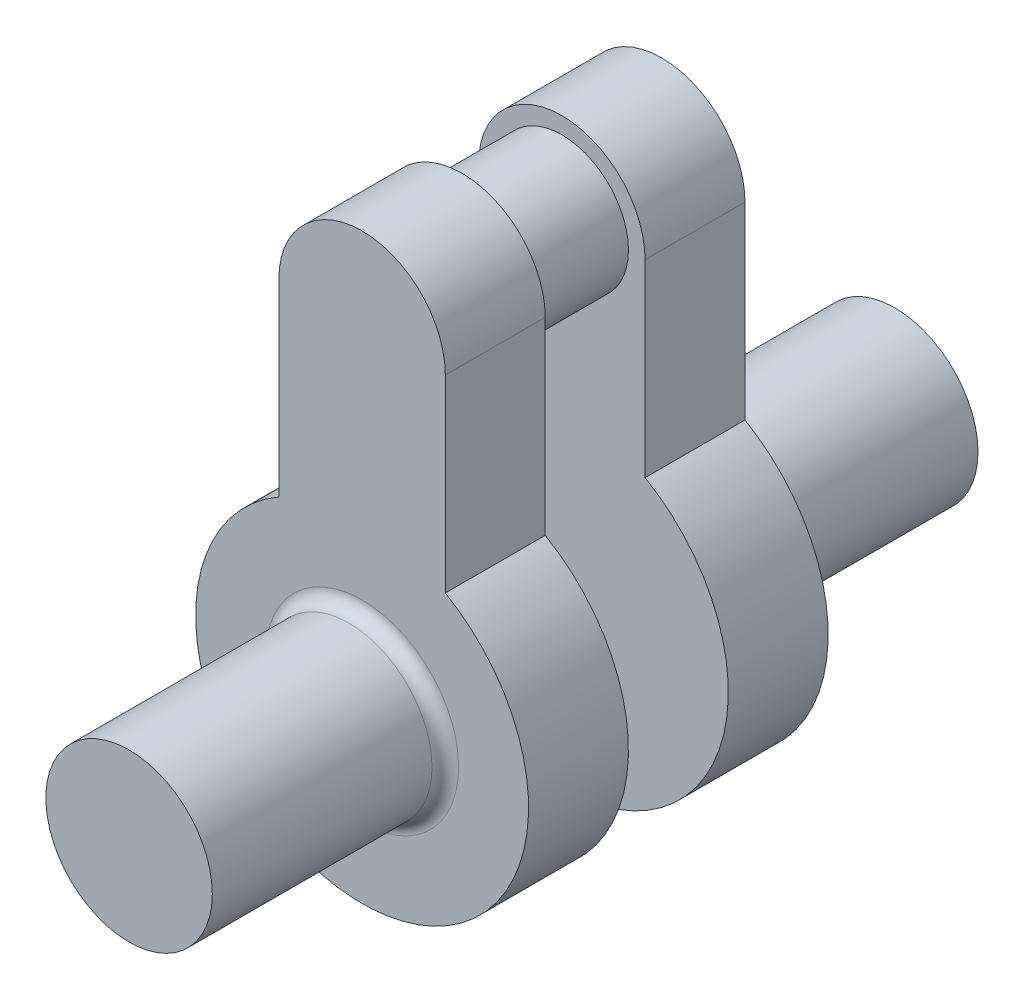
SolidWorks part; units mm, degrees
ref_plane "Ön Düzlem" through (0, 0, 0) normal (0, 0, 1) x (1, 0, 0)
ref_plane "Üst Düzlem" through (0, 0, 0) normal (0, 1, 0) x (1, 0, 0)
ref_plane "Sağ Düzlem" through (0, 0, 0) normal (1, 0, 0) x (0, 0, -1)
sketch "Sketch1" plane through (0, 0, 0) normal (0, 0, 1) x (1, 0, 0)
  line L0 (-12.5, 50) -> (-12.5, 21.6506)
  line L1 (12.5, 50) -> (12.5, 21.6506)
  arc A0 (-12.5, 21.6506) -> (12.5, 21.6506) centre (0, 0) ccw
  arc A3 (12.5, 50) -> (-12.5, 50) centre (0, 50) ccw
  dimension "D1" = 50
  dimension "D2" = 25
  dimension "D3" = 50
extrude "Boss-Extrude1" add sketch "Sketch1" along normal blind 15
sketch "Sketch2" plane through (0, 0, 15) normal (0, 0, 1) x (1, 0, 0)
  circle A0 centre (0, 0) radius 12.5
  dimension "D1" = 25
extrude "Boss-Extrude2" add sketch "Sketch2" along normal blind 35
fillet "Fillet1" radius 2 1 edges at (12.5, 0, 15)
sketch "Sketch3" plane through (0, 0, 0) normal (0, 0, -1) x (-1, 0, 0)
  circle A0 centre (0, 50) radius 10
  dimension "D1" = 20
extrude "Boss-Extrude3" add sketch "Sketch3" along normal blind 15
ref_plane "Plane1" through (0, 0, -7.5) normal (0, 0, 1) x (1, 0, 0)
mirror "Mirror1" about plane through (0, 0, -7.5) normal (0, 0, 1) of "Fillet1", "Boss-Extrude2", "Boss-Extrude1"
